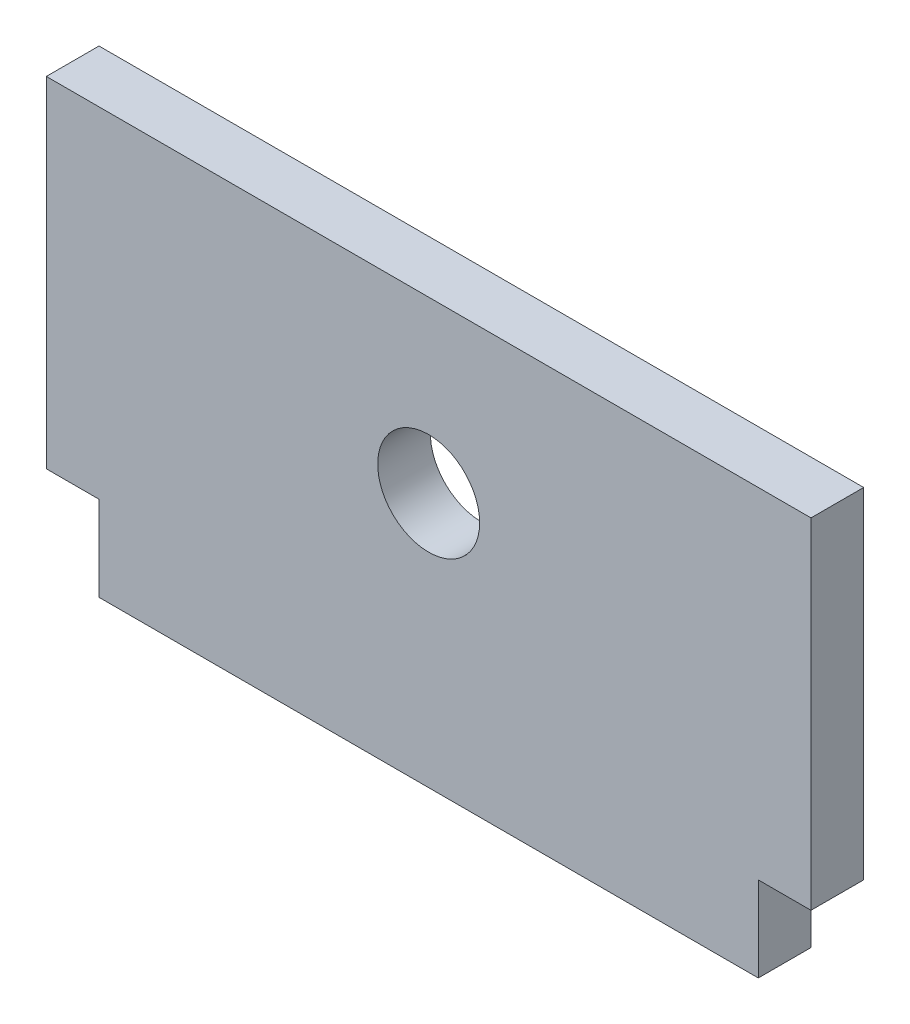
SolidWorks part; units mm, degrees
material "Teak"
ref_plane "Front Plane" through (0, 0, 0) normal (0, 0, 1) x (1, 0, 0)
ref_plane "Top Plane" through (0, 0, 0) normal (0, 1, 0) x (1, 0, 0)
ref_plane "Right Plane" through (0, 0, 0) normal (1, 0, 0) x (0, 0, -1)
sketch "Sketch1" plane through (0, 0, 0) normal (0, 0, 1) x (1, 0, 0)
  line L1 (-22.5, -10) -> (22.5, -10)
  line L2 (-22.5, -10) -> (-22.5, 10)
  line L3 (-22.5, 10) -> (22.5, 10)
  line L4 (22.5, -10) -> (22.5, 10)
  line L5 (-22.5, -10) -> (22.5, 10) construction
  line L6 (-22.5, 10) -> (22.5, -10) construction
  circle A0 centre (0, 0) radius 3
  point P0 (0, 0)
  dimension "D3" = 6
  dimension "D1" = 20
  dimension "D2" = 45
extrude "Boss-Extrude1" add sketch "Sketch1" along normal blind 3.1
sketch "Sketch2" plane through (0, 0, 3.1) normal (0, 0, 1) x (1, 0, 0)
  line L0 (-19.4, -10) -> (19.4, -10)
  line L1 (-19.4, -10) -> (-19.4, -15)
  line L2 (19.4, -10) -> (19.4, -15)
  line L3 (-19.4, -15) -> (19.4, -15)
  line L4 (-22.5, -10) -> (22.5, -10) construction
  line L5 (-22.5, 10) -> (-22.5, -10) construction
  dimension "D1" = 3.1
  dimension "D2" = 3.1
  dimension "D3" = 5
extrude "Boss-Extrude2" add sketch "Sketch2" against normal through all
equation "\"thick\" = 3.1mm"
equation "\"small_bearing_outer\"=12.9mm"
equation "\"servo1_L\"=40.7mm"
equation "\"servo1_W\"=20.5mm"
equation "\"servo1_H\"=43.5mm"
equation "\"servo1_hL\"=49mm"
equation "\"servo1_hW\"=10mm"
equation "\"servo1_H2\"=27mm"
equation "\"large_bearing_inner\"=2.75in"
equation "\"large_bearing_outer\"=4.75in"
equation "\"large_bearing_thick\"=3/8in"
equation "\"large_bearing_h1\"=3.25in"
equation "\"large_bearing_h2\"=4.25in"
equation "\"D1@Boss-Extrude1\"=\"thick\""
equation "\"D1@Sketch2\"=\"thick\""
equation "\"D2@Sketch2\"=\"D1@Sketch2\""
